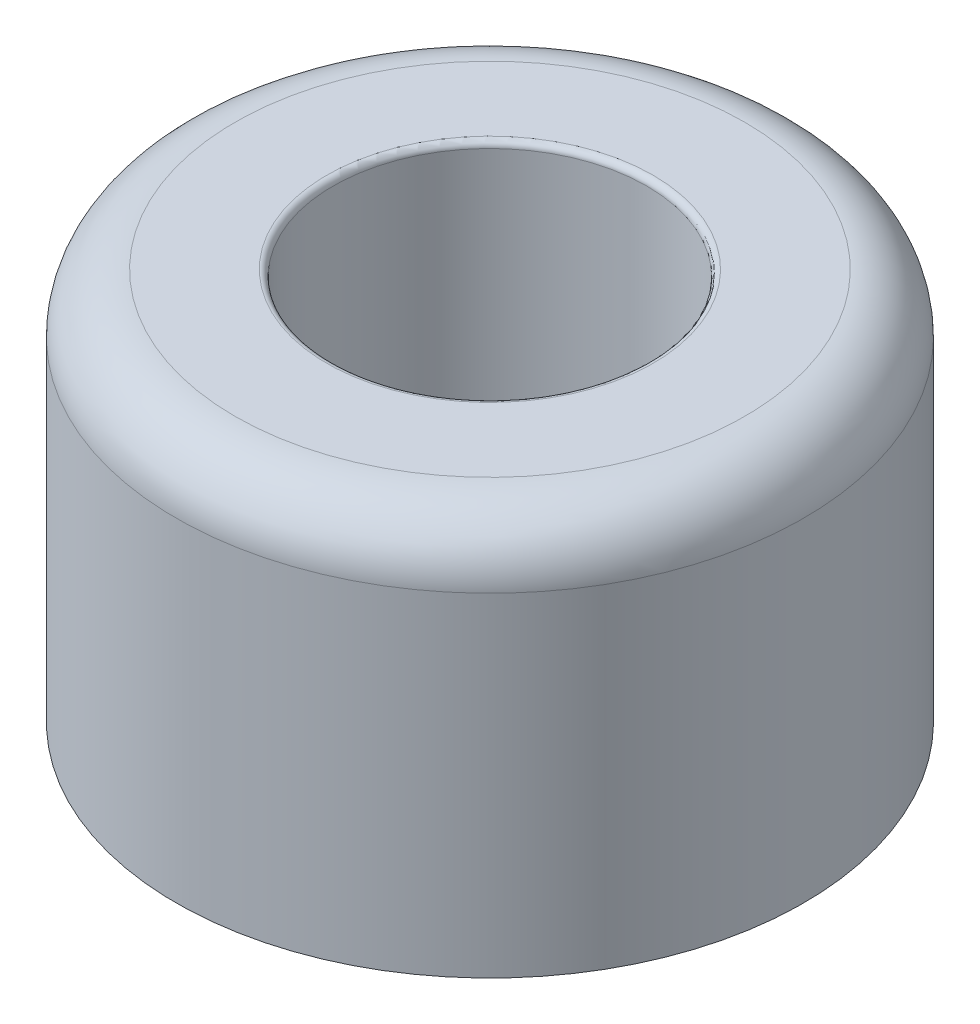
SolidWorks part; units mm, degrees
ref_plane "Front" through (0, 0, 0) normal (0, 0, 1) x (1, 0, 0)
ref_plane "Top" through (0, 0, 0) normal (0, 1, 0) x (1, 0, 0)
ref_plane "Right" through (0, 0, 0) normal (1, 0, 0) x (0, 0, -1)
sketch "Sketch1" plane through (0, 0, 0) normal (0, 0, 1) x (1, 0, 0)
  line L0 (6.35, 0) -> (-6.35, 0) construction
  line L1 (0, 0) -> (0, 7.9375) construction
  line L2 (3.175, 3.175) -> (-3.175, 3.175) construction
  line L3 (1.9844, 0) -> (-1.9844, 0) construction
  point P7 (0, 3.175)
  dimension "OD" = 12.7
  dimension "Height" = 7.9375
  dimension "Counterbore Dia" = 6.35
  dimension "Mounting Surface Ht" = 3.175
  dimension "Mounting Hole Dia" = 3.9688
sketch "Sketch2" plane through (0, 0, 0) normal (0, 0, 1) x (1, 0, 0)
  line L0 (-6.35, 0) -> (-6.35, 6.7469)
  line L1 (-5.1594, 7.9375) -> (-3.175, 7.9375)
  line L2 (-3.175, 7.9375) -> (-3.175, 3.175)
  line L3 (-3.175, 3.175) -> (-1.9844, 3.175)
  line L4 (3.175, 3.175) -> (-3.175, 3.175) construction
  line L5 (-1.9844, 3.175) -> (-1.9844, 0)
  line L6 (-1.9844, 0) -> (-6.35, 0)
  arc A0 (-5.1594, 7.9375) -> (-6.35, 6.7469) centre (-5.1594, 6.7469) ccw
  dimension "D1" = 1.1906
revolve "Revolve1" add sketch "Sketch2" angle 360 about L1
fillet "Fillet1" radius 0.127 1 edges at (0, 7.9375, -3.175)
sketch "Sketch3" plane through (0, 0, 0) normal (0, 0, 1) x (1, 0, 0)
  line L0 (-1.9844, 3.175) -> (-1.9844, 0) construction
  line L1 (1.9844, 0) -> (1.9844, 3.175) construction
  line L2 (-3.175, 7.8105) -> (-3.175, 3.175) construction
  line L3 (3.175, 3.175) -> (3.175, 7.8105) construction
  line L4 (-1.9844, 3.175) -> (-1.9844, 0)
  line L5 (1.9844, 0) -> (1.9844, 3.175)
  line L6 (-3.175, 7.8105) -> (-3.175, 3.175)
  line L7 (3.175, 3.175) -> (3.175, 7.8105)
  line L8 (-3.175, 3.175) -> (-1.9844, 3.175)
  line L9 (1.9844, 3.175) -> (3.175, 3.175)
  arc A0 (-3.175, 7.8105) -> (-3.302, 7.9375) centre (-3.302, 7.8105) ccw construction
  arc A1 (3.302, 7.9375) -> (3.175, 7.8105) centre (3.302, 7.8105) ccw construction
  arc A2 (-3.175, 7.8105) -> (-3.302, 7.9375) centre (-3.302, 7.8105) ccw
  arc A3 (3.302, 7.9375) -> (3.175, 7.8105) centre (3.302, 7.8105) ccw
equation "\"D1@Sketch2\"=\"Height@Sketch1\"*.15"
equation "\"D1@Fillet1\"=\"OD@Sketch1\"*.01"
